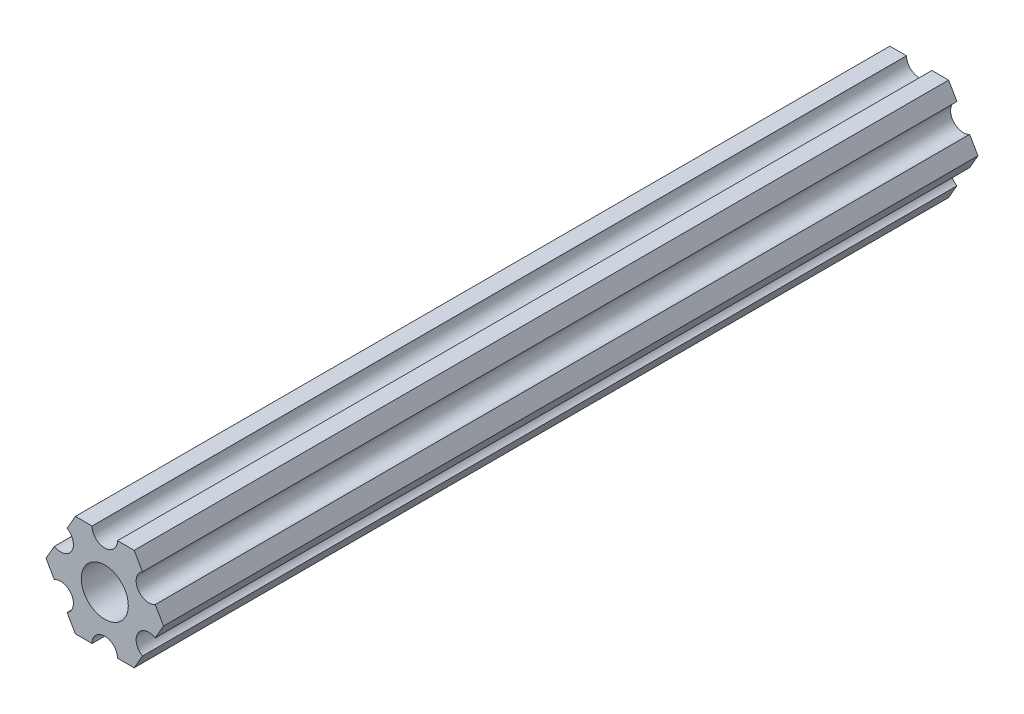
SolidWorks part; units mm, degrees
ref_plane "Front Plane" through (0, 0, 0) normal (0, 0, 1) x (1, 0, 0)
ref_plane "Top Plane" through (0, 0, 0) normal (0, 1, 0) x (1, 0, 0)
ref_plane "Right Plane" through (0, 0, 0) normal (1, 0, 0) x (0, 0, -1)
sketch "Sketch1" plane through (0, 0, 0) normal (0, 0, 1) x (1, 0, 0)
  line L0 (-1.5875, 6.35) -> (-3.6662, 6.35)
  line L1 (7.3323, 0) -> (6.293, 1.8002)
  line L2 (3.6662, 6.35) -> (1.5875, 6.35)
  line L3 (-3.6662, 6.35) -> (-4.7055, 4.5498)
  line L4 (-7.3323, 0) -> (-6.293, -1.8002)
  line L5 (-3.6662, -6.35) -> (-1.5875, -6.35)
  line L6 (3.6662, -6.35) -> (4.7055, -4.5498)
  line L7 (-6.293, 1.8002) -> (-7.3323, 0)
  line L8 (-4.7055, -4.5498) -> (-3.6662, -6.35)
  line L9 (1.5875, -6.35) -> (3.6662, -6.35)
  line L10 (6.293, -1.8002) -> (7.3323, 0)
  line L11 (4.7055, 4.5498) -> (3.6662, 6.35)
  circle A0 centre (0, 0) radius 2.9337
  arc A2 (-1.5875, 6.35) -> (1.5875, 6.35) centre (0, 6.35) ccw
  arc A3 (4.7055, 4.5498) -> (6.293, 1.8002) centre (5.4993, 3.175) ccw
  arc A4 (6.293, -1.8002) -> (4.7055, -4.5498) centre (5.4993, -3.175) ccw
  arc A5 (1.5875, -6.35) -> (-1.5875, -6.35) centre (0, -6.35) ccw
  arc A6 (-4.7055, -4.5498) -> (-6.293, -1.8002) centre (-5.4993, -3.175) ccw
  arc A7 (-6.293, 1.8002) -> (-4.7055, 4.5498) centre (-5.4993, 3.175) ccw
  dimension "D1" = 5.8674
  dimension "D3" = 3.175
  dimension "D4" = 6
extrude "Boss-Extrude1" add sketch "Sketch1" along normal blind 101.6
